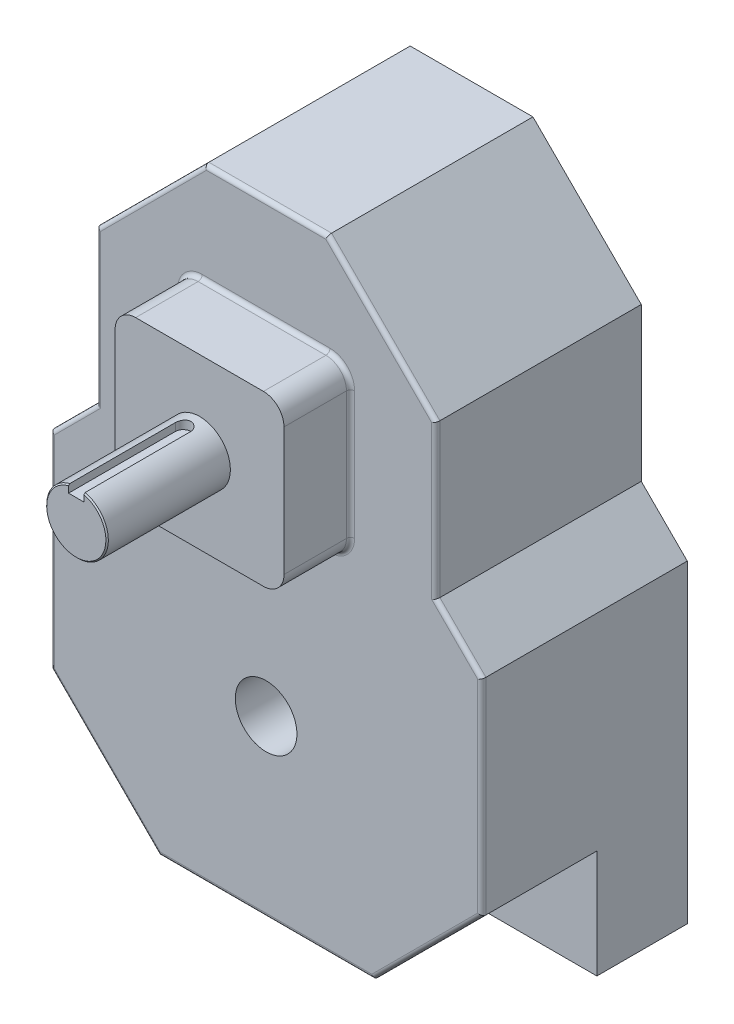
SolidWorks part; units mm, degrees
ref_plane "Front Plane" through (0, 0, 0) normal (0, 0, 1) x (1, 0, 0)
ref_plane "Top Plane" through (0, 0, 0) normal (0, 1, 0) x (1, 0, 0)
ref_plane "Right Plane" through (0, 0, 0) normal (1, 0, 0) x (0, 0, -1)
ref_plane "G" through (0, 107.95, 0) normal (0, 1, 0) x (-1, 0, 0)
ref_plane "E" through (0, 188.976, 0) normal (0, 1, 0) x (-1, 0, 0)
ref_plane "J" through (0, 246.126, 0) normal (0, 1, 0) x (-1, 0, 0)
ref_plane "B" through (0, 0, 63.5) normal (0, 0, 1) x (1, 0, 0)
ref_plane "C" through (0, 0, 122.174) normal (0, 0, 1) x (1, 0, 0)
ref_plane "A" through (0, 0, 84.074) normal (0, 0, 1) x (1, 0, 0)
sketch "L,M" plane through (0, 0, 0) normal (0, 0, 1) x (1, 0, 0)
  line L0 (66.3179, 246.126) -> (-18.9733, 246.126) construction
  line L1 (0, 0) -> (0, 107.95) construction
  line L2 (48.895, 107.95) -> (-48.895, 107.95) construction
  line L3 (-66.675, 53.975) -> (66.675, 53.975)
  line L4 (-18.9733, 246.126) -> (18.9733, 246.126)
  line L5 (48.895, 246.126) -> (-48.895, 246.126) construction
  line L6 (18.9733, 246.126) -> (52.451, 212.6483)
  line L7 (52.451, 212.6483) -> (52.451, 165.3037)
  line L8 (52.451, 165.3037) -> (66.675, 151.0797)
  line L9 (66.675, 151.0797) -> (66.675, 53.975)
  line L11 (66.3179, 246.126) -> (18.9733, 246.126) construction
  line L12 (-66.675, 151.0797) -> (-66.675, 53.975)
  line L13 (-52.451, 165.3037) -> (-66.675, 151.0797)
  line L14 (-52.451, 212.6483) -> (-52.451, 165.3037)
  line L15 (-18.9733, 246.126) -> (-52.451, 212.6483)
  line L16 (48.895, 188.976) -> (-48.895, 188.976) construction
  point P0 (-52.451, 188.976)
  point P7 (0, 53.975)
  point P23 (0, 246.126)
  dimension "D1" = 104.902
  dimension "D2" = 133.35
  dimension "D3" = 45
extrude "Boss-Extrude1" add sketch "L,M" along normal up to surface (63.5 mm away) up to plane "B"
sketch "Sketch3" plane through (0, 0, 63.5) normal (0, 0, 1) x (1, 0, 0)
  line L1 (48.895, 188.976) -> (-48.895, 188.976) construction
  line L2 (-26.0985, 215.0745) -> (26.0985, 215.0745)
  line L3 (-26.0985, 215.0745) -> (-26.0985, 162.8775)
  line L4 (-26.0985, 162.8775) -> (26.0985, 162.8775)
  line L5 (26.0985, 215.0745) -> (26.0985, 162.8775)
  line L6 (0, 188.976) -> (0, 0) construction
  line L7 (-26.0985, 215.0745) -> (26.0985, 162.8775) construction
  point P4 (0, 188.976)
  dimension "D1" = 52.197
extrude "Boss-Extrude2" add sketch "Sketch3" along normal up to surface (20.574 mm away) up to plane "A"
sketch "D" plane through (0, 0, 84.074) normal (0, 0, 1) x (1, 0, 0)
  line L0 (-26.0985, 215.0745) -> (26.0985, 162.8775) construction
  circle A0 centre (0, 188.976) radius 9.525
  dimension "D1" = 19.05
extrude "Boss-Extrude3" add sketch "D" along normal up to surface (38.1 mm away) up to plane "C"
sketch "Sketch5" plane through (0, 0, 63.5) normal (0, 0, 1) x (1, 0, 0)
  line L0 (66.675, 87.4527) -> (33.1973, 53.975)
  line L1 (66.675, 53.975) -> (66.675, 151.0797) construction
  line L2 (-66.675, 53.975) -> (66.675, 53.975) construction
  line L3 (33.1973, 53.975) -> (66.675, 53.975)
  line L4 (66.675, 53.975) -> (66.675, 87.4527)
  line L5 (-18.9733, 246.126) -> (-52.451, 212.6483) construction
  line L6 (0, 53.975) -> (0, 188.976) construction
  line L7 (-66.675, 53.975) -> (-66.675, 87.4527)
  line L8 (-33.1973, 53.975) -> (-66.675, 53.975)
  line L9 (-66.675, 87.4527) -> (-33.1973, 53.975)
extrude "Cut-Extrude1" cut sketch "Sketch5" against normal blind 35.56
fillet "Fillet1" radius 6.35 4 edges at (-26.0985, 162.8775, 73.787) (26.0985, 162.8775, 73.787) (-26.0985, 215.0745, 73.787) (26.0985, 215.0745, 73.787)
fillet "Fillet2" radius 1.27 20 edges at (24.2386, 164.7374, 63.5) (26.0985, 188.976, 63.5) (24.2386, 213.2146, 63.5) (0, 215.0745, 63.5) (-24.2386, 213.2146, 63.5) (-26.0985, 188.976, 63.5) (-24.2386, 164.7374, 63.5) (0, 162.8775, 63.5) (-66.675, 119.2662, 63.5) (-59.563, 158.1917, 63.5) (-52.451, 188.976, 63.5) (-35.7122, 229.3872, 63.5) (0, 246.126, 63.5) (35.7122, 229.3872, 63.5) (52.451, 188.976, 63.5) (59.563, 158.1917, 63.5) (66.675, 119.2662, 63.5) (49.9362, 70.7138, 63.5) (0, 53.975, 63.5) (-49.9362, 70.7138, 63.5)
sketch "Sketch6" plane through (0, 188.976, 0) normal (0, 1, 0) x (-1, 0, 0)
  line L0 (0, 122.174) -> (0, 89.154) construction
  line L1 (48.895, 122.174) -> (-48.895, 122.174) construction
  line L2 (2.3876, 122.174) -> (2.3876, 89.154)
  line L3 (-2.3876, 122.174) -> (-2.3876, 89.154)
  line L4 (0, 0) -> (0, 89.154) construction
  line L6 (-18.9733, 0) -> (18.9733, 0) construction
  line L7 (48.895, 84.074) -> (-48.895, 84.074) construction
  arc A0 (2.3876, 122.174) -> (-2.3876, 122.174) centre (0, 122.174) ccw
  arc A1 (-2.3876, 89.154) -> (2.3876, 89.154) centre (0, 89.154) ccw
  point P4 (0, 105.664)
  dimension "D2" = 5.08
  dimension "D1" = 4.7752
extrude "Keyway" cut sketch "Sketch6" along normal through all from offset 6.8326
chamfer "Chamfer1" distance 0.381 angle 45 1 edges at (0, 179.451, 122.174)
sketch "Sketch7" plane through (0, 0, 0) normal (0, 0, -1) x (-1, 0, 0)
  line L0 (48.895, 107.95) -> (-48.895, 107.95) construction
  line L1 (0, 107.95) -> (0, 188.976) construction
  circle A0 centre (0, 107.95) radius 9.525
  circle A1 centre (0, 188.976) radius 9.525 construction
extrude "Cut-Extrude3" cut sketch "Sketch7" against normal through all
